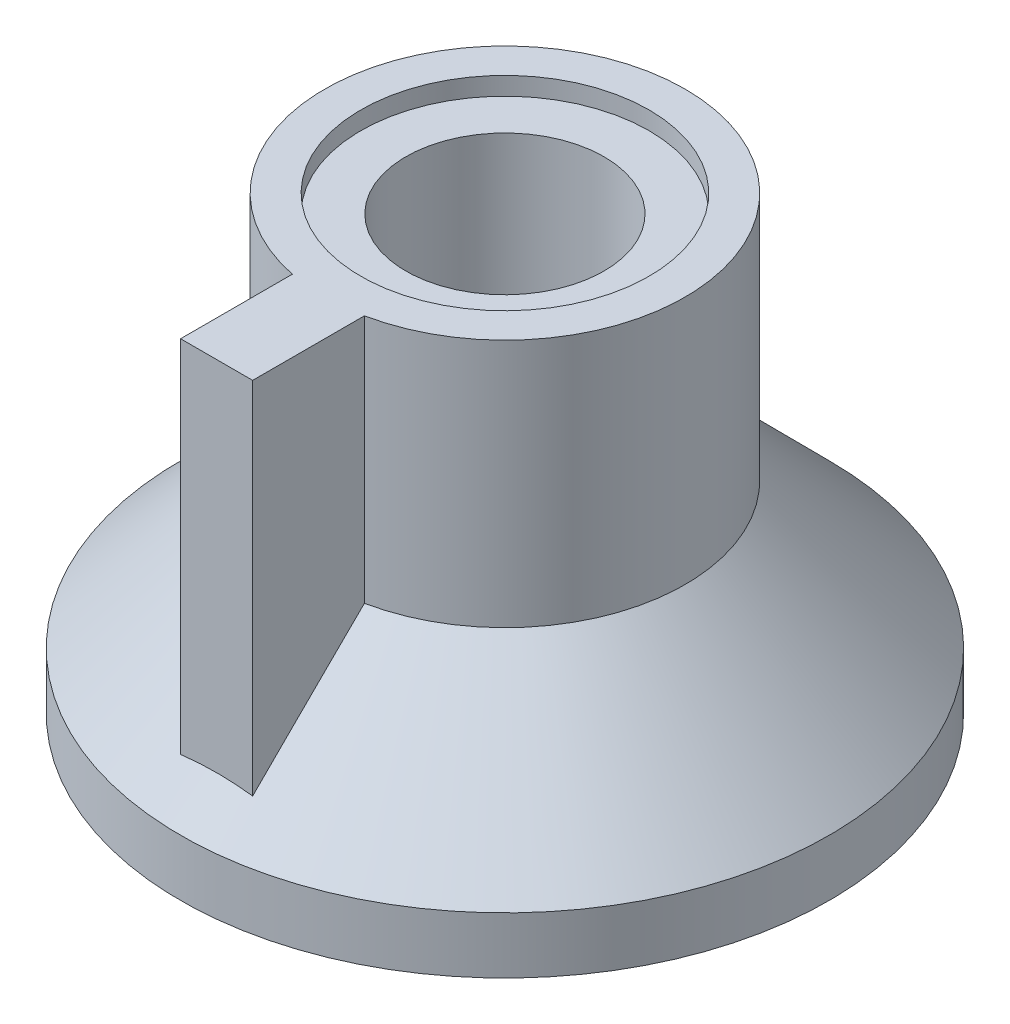
SolidWorks part; units mm, degrees
ref_plane "Front Plane" through (0, 0, 0) normal (0, 0, 1) x (1, 0, 0)
ref_plane "Top Plane" through (0, 0, 0) normal (0, 1, 0) x (1, 0, 0)
ref_plane "Right Plane" through (0, 0, 0) normal (1, 0, 0) x (0, 0, -1)
sketch "Sketch1" plane through (0, 0, 0) normal (1, 0, 0) x (0, 0, -1)
  line L0 (0, 0) -> (0, 10) construction
  line L1 (-4, 14.0884) -> (-4, 14.5884)
  line L2 (-5, 14.5884) -> (-5, 7.6799)
  line L3 (-5, 7.6799) -> (-9, 3.6555)
  line L4 (-9, 3.6555) -> (-9, 2.0884)
  line L5 (-9, 2.0884) -> (-6, 2.0884)
  line L6 (-2.75, 4.5091) -> (-2.75, 14.0884)
  line L7 (-2.75, 14.0884) -> (-4, 14.0884)
  line L8 (-4, 14.5884) -> (-5, 14.5884)
  line L9 (-6, 2.0884) -> (-6, 4.5091)
  line L12 (-6, 4.5091) -> (-2.75, 4.5091)
  point P12 (-6, 4.5091)
  point P13 (-5.8552, 4.5091)
  point P15 (-4.5, 14.5884)
  dimension "D1" = 5.5
  dimension "D2" = 10
  dimension "D3" = 1
  dimension "D4" = 12
  dimension "D5" = 18
  dimension "D6" = 12
  dimension "D7" = 0.5
revolve "Revolve1" add sketch "Sketch1" angle 360 about L0
ref_plane "Plane1" through (0, 0, 8) normal (0, 0, 1) x (1, 0, 0)
sketch "Sketch2" plane through (0, 0, 8) normal (0, 0, 1) x (1, 0, 0)
  line L0 (0, 2.0884) -> (0, 14.5884) construction
  line L1 (-9, 2.0884) -> (9, 2.0884) construction
  line L2 (4, 14.5884) -> (-4, 14.5884) construction
  line L4 (-1, 2.0884) -> (1, 2.0884)
  line L5 (-1, 2.0884) -> (-1, 14.5884)
  line L6 (-1, 14.5884) -> (1, 14.5884)
  line L7 (1, 2.0884) -> (1, 14.5884)
  line L8 (-1, 2.0884) -> (1, 14.5884) construction
  line L9 (-1, 14.5884) -> (1, 2.0884) construction
  point P6 (0, 8.3384)
  dimension "D1" = 2
extrude "Boss-Extrude1" add sketch "Sketch2" against normal blind 3.5
sketch "Sketch3" plane through (0, 0, 0) normal (1, 0, 0) x (0, 0, -1)
  line L0 (0, 14.0884) -> (0, 0) construction
  line L1 (4, 14.0884) -> (-4, 14.0884) construction
  line L2 (0, 4.5091) -> (6.0408, 4.5091)
  line L3 (-2.75, 4.5091) -> (2.75, 4.5091) construction
  line L4 (6.0408, 4.5091) -> (6.0408, 1.1952)
  line L5 (6.0408, 1.1952) -> (0, 1.1952)
  line L6 (0, 1.1952) -> (0, 4.5091)
revolve "Cut-Revolve1" cut sketch "Sketch3" angle 360 about L6
